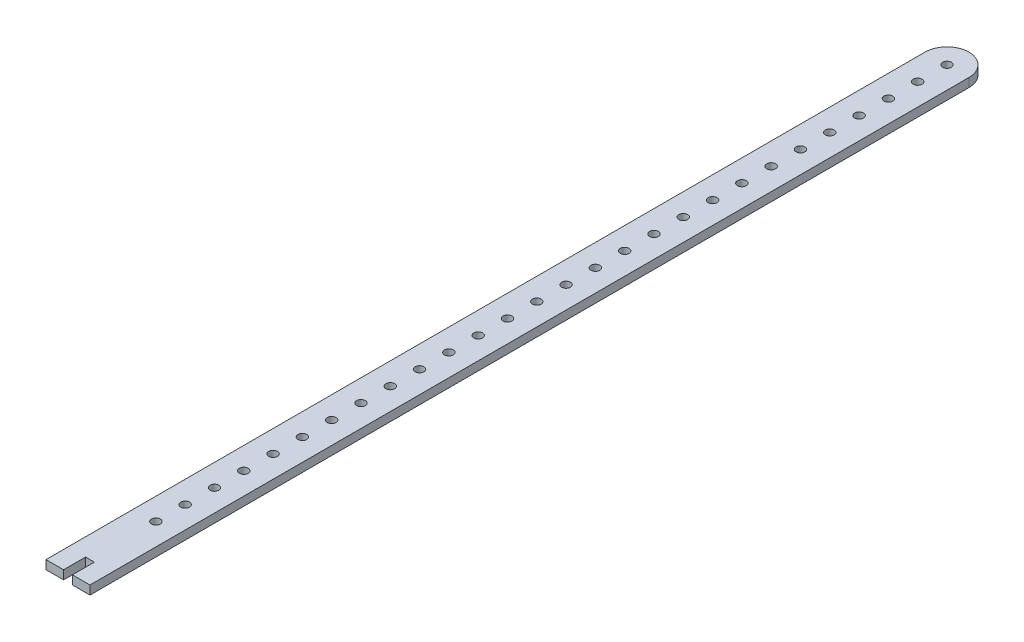
SolidWorks part; units mm, degrees
ref_plane "Спереди" through (0, 0, 0) normal (0, 0, 1) x (1, 0, 0)
ref_plane "Сверху" through (0, 0, 0) normal (0, 1, 0) x (1, 0, 0)
ref_plane "Справа" through (0, 0, 0) normal (1, 0, 0) x (0, 0, -1)
sketch "Эскиз1" plane through (0, 0, 0) normal (0, 1, 0) x (1, 0, 0)
  line L0 (0, -1000) -> (0, 49000) construction
  line L1 (-15, -300) -> (-3, -300)
  line L2 (-15, -300) -> (-15, 300)
  line L3 (0, 300) -> (0, 280) construction
  line L4 (15, -300) -> (15, 300)
  line L5 (-15, -300) -> (15, 300) construction
  line L6 (-15, 300) -> (15, -300) construction
  line L7 (3, -300) -> (15, -300)
  line L9 (-3, -300) -> (-3, -285)
  line L10 (-3, -285) -> (3, -285)
  line L11 (3, -300) -> (3, -285)
  line L12 (0, -300) -> (3, -285) construction
  line L13 (-3, -285) -> (0, -300) construction
  arc A0 (15, 300) -> (-15, 300) centre (0, 300) ccw
  circle A1 centre (0, 300) radius 3
  circle A2 centre (0, 280) radius 3
  circle A3 centre (0, 260) radius 3
  circle A4 centre (0, 240) radius 3
  circle A5 centre (0, 220) radius 3
  circle A6 centre (0, 200) radius 3
  circle A7 centre (0, 180) radius 3
  circle A8 centre (0, 160) radius 3
  circle A9 centre (0, 140) radius 3
  circle A10 centre (0, 120) radius 3
  circle A11 centre (0, 100) radius 3
  circle A12 centre (0, 80) radius 3
  circle A13 centre (0, 60) radius 3
  circle A14 centre (0, 40) radius 3
  circle A15 centre (0, 20) radius 3
  circle A16 centre (0, 0) radius 3
  circle A17 centre (0, -20) radius 3
  circle A18 centre (0, -40) radius 3
  circle A19 centre (0, -60) radius 3
  circle A20 centre (0, -80) radius 3
  circle A21 centre (0, -100) radius 3
  circle A22 centre (0, -120) radius 3
  circle A23 centre (0, -140) radius 3
  circle A24 centre (0, -160) radius 3
  circle A25 centre (0, -180) radius 3
  circle A26 centre (0, -200) radius 3
  circle A27 centre (0, -220) radius 3
  circle A28 centre (0, -240) radius 3
  point P0 (0, 0)
  point P10 (0, -300)
  dimension "D3" = 28
  dimension "D1" = 600
  dimension "D2" = 30
  dimension "D4" = 20
  dimension "D5" = 6
extrude "Бобышка-Вытянуть1" add sketch "Эскиз1" along normal blind 6
